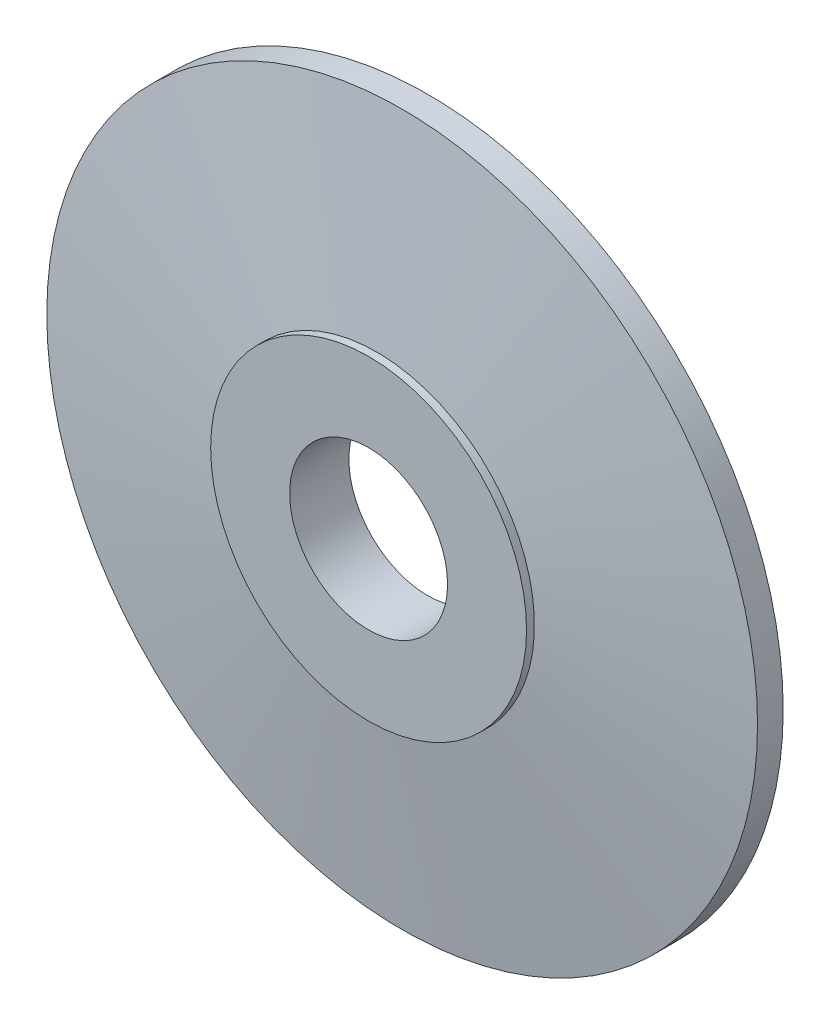
SolidWorks part; units mm, degrees
material "ABS"
ref_plane "Спереди" through (0, 0, 0) normal (0, 0, 1) x (1, 0, 0)
ref_plane "Сверху" through (0, 0, 0) normal (0, 1, 0) x (1, 0, 0)
ref_plane "Справа" through (0, 0, 0) normal (1, 0, 0) x (0, 0, -1)
sketch "Эскиз1" plane through (0, 0, 0) normal (0, 0, 1) x (1, 0, 0)
  circle A0 centre (0, 0) radius 9
  circle A1 centre (0, 0) radius 2
  dimension "D1" = 4
  dimension "D2" = 18
extrude "Бобышка-Вытянуть1" add sketch "Эскиз1" along normal blind 1.3
sketch "Эскиз2" plane through (0, 0, 1.3) normal (0, 0, 1) x (1, 0, 0)
  circle A0 centre (0, 0) radius 4
  circle A1 centre (0, 0) radius 2
  circle A2 centre (0, 0) radius 2 construction
  dimension "D1" = 8
extrude "Бобышка-Вытянуть2" add sketch "Эскиз2" along normal blind 0.2
sketch "Эскиз3" plane through (0, 0, 0) normal (0, 1, 0) x (1, 0, 0)
  line L0 (-4, -1.3) -> (-9, -0.65)
  line L1 (-9, 0) -> (-9, -1.3) construction
  line L2 (-9, -0.65) -> (-9, -1.3)
  line L3 (-9, -1.3) -> (-4, -1.3)
  line L4 (0, 0) -> (0, -2.9752) construction
revolve "Вырез-Повернуть1" cut sketch "Эскиз3" angle 360 about L4
